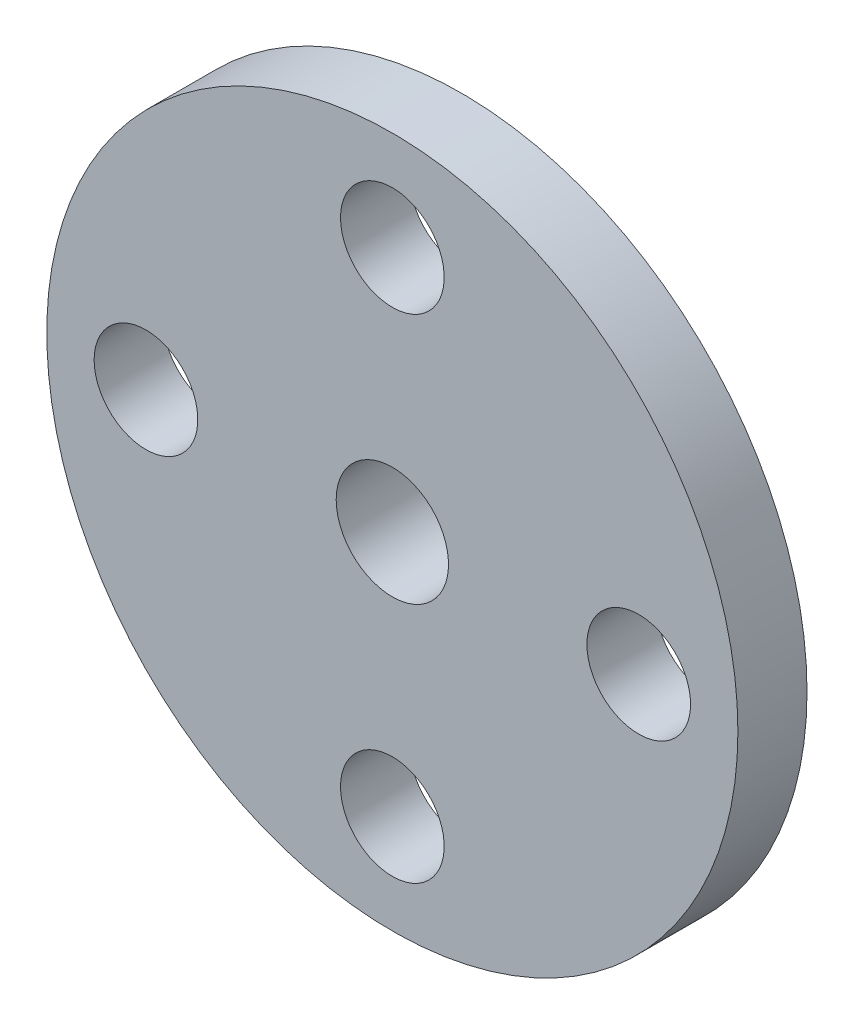
SolidWorks part; units mm, degrees
ref_plane "Piano frontale" through (0, 0, 0) normal (0, 0, 1) x (1, 0, 0)
ref_plane "Piano superiore" through (0, 0, 0) normal (0, 1, 0) x (1, 0, 0)
ref_plane "Piano destro" through (0, 0, 0) normal (1, 0, 0) x (0, 0, -1)
sketch "Schizzo14" plane through (0, 0, 0) normal (0, 0, 1) x (1, 0, 0)
  line L0 (0, 10) -> (0, -10) construction
  line L1 (0, -10) -> (-10, 0) construction
  line L2 (-10, 0) -> (10, 0) construction
  circle A0 centre (0, 0) radius 10
  dimension "D1" = 20
extrude "Estrusione-Estrusione2" add sketch "Schizzo14" along normal blind 2
hole_wizard "Foro Ø3.0 (3)-1" positions "Schizzo3D14" profile "Schizzo18" hole size "Ø3.0" standard "ISO" end condition through all
sketch3d "Schizzo3D14"
  point P0 (7.13, 0, 0)
  point P2 (-7.13, 0, 0)
  point P4 (0, -7.13, 0)
  point P6 (0, 7.13, 0)
  dimension "D1" = 7.13
  dimension "D2" = 7.13
  dimension "D3" = 7.13
  dimension "D4" = 7.13
sketch "Schizzo18" plane through (7.13, 0, 0) normal (1, 0, 0) x (0, 1, 0)
  line L0 (0, 0) -> (0, 2)
  line L1 (0, 2) -> (1.5, 2)
  line L2 (1.5, 2) -> (1.5, 0)
  line L5 (1.5, 0) -> (0, 0)
  line L11 (0, -6.35) -> (0, 107.95) construction
  dimension "Thru Hole Dia." = 3
  dimension "Thru Hole Depth" = 2
cosmetic thread "Filettatura cosmetica2" parameters "D1"=1.9999, "D2"=3
cosmetic thread "Filettatura cosmetica4" parameters "D1"=1.9999, "D2"=3
cosmetic thread "Filettatura cosmetica5" parameters "D1"=1.9999, "D2"=3
sketch "Schizzo19" plane through (0, 0, 0) normal (0, 0, 1) x (1, 0, 0)
  circle A0 centre (0, 0) radius 4.5
  dimension "D1" = 9
extrude "Estrusione-Estrusione3" add sketch "Schizzo19" against normal blind 2
sketch "Schizzo20" plane through (0, 0, -2) normal (0, 0, -1) x (-1, 0, 0)
  circle A0 centre (0, 0) radius 1.625
  dimension "D1" = 3.25
extrude "Taglio-Estrusione1" cut sketch "Schizzo20" against normal through all
